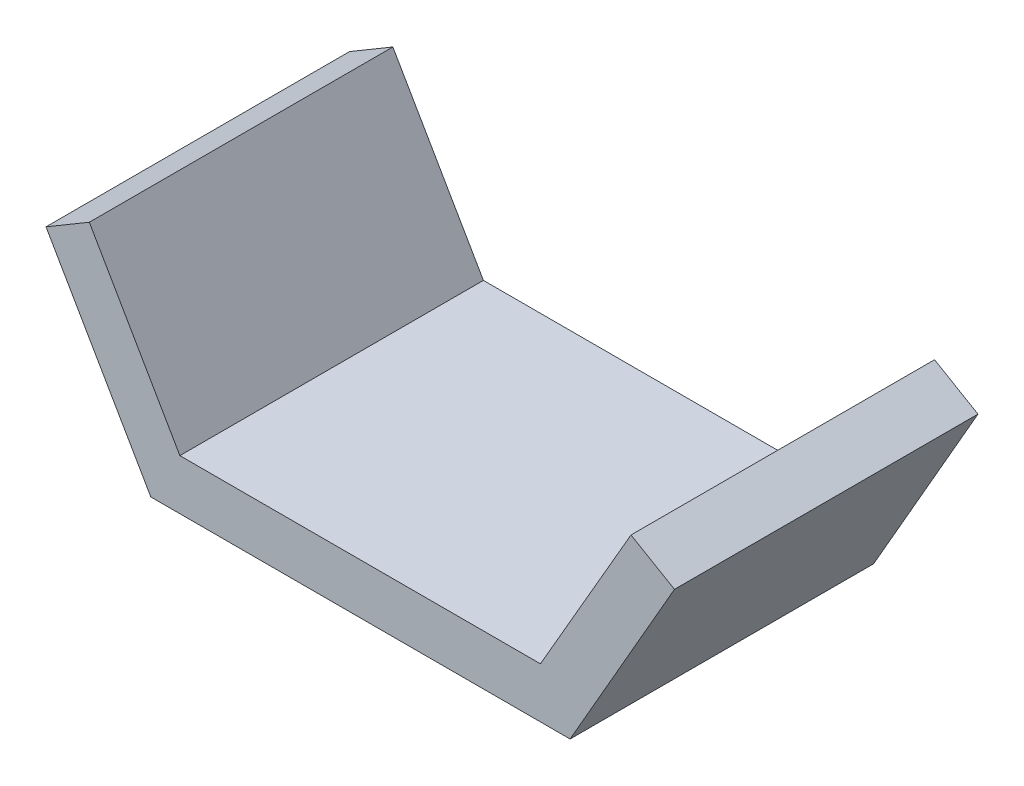
SolidWorks part; units mm, degrees
ref_plane "Alzado" through (0, 0, 0) normal (0, 0, 1) x (1, 0, 0)
ref_plane "Planta" through (0, 0, 0) normal (0, 1, 0) x (1, 0, 0)
ref_plane "Vista lateral" through (0, 0, 0) normal (1, 0, 0) x (0, 0, -1)
sketch "Croquis1" plane through (0, 0, 0) normal (0, 0, 1) x (1, 0, 0)
  line L8 (-113.3457, -408.1893) -> (2036.6543, -408.1893)
  line L9 (-113.3457, -408.1893) -> (-653.3457, 527.1182)
  line L10 (-653.3457, 527.1182) -> (-911.5508, 374.3425)
  line L11 (-911.5508, 374.3425) -> (-286.5508, -708.1893)
  line L12 (-286.5508, -708.1893) -> (2213.4492, -708.1893)
  line L13 (2213.4492, -708.1893) -> (2835.752, 375.8952)
  line L14 (2835.752, 375.8952) -> (2576.6543, 527.1182)
  line L15 (2576.6543, 527.1182) -> (2036.6543, -408.1893)
  point P2 (-667.2584, 608.9352)
  point P9 (-531.8495, 707.7471)
  dimension "D1" = 2150
  dimension "D2" = 2500
  dimension "D3" = 1250
  dimension "D4" = 1250
  dimension "D5" = 1080
  dimension "D6" = 1080
  dimension "D7" = 300
  dimension "D8" = 300
  dimension "D9" = 120
  dimension "D10" = 120
  dimension "D11" = 300
extrude "Saliente-Extruir1" add sketch "Croquis1" along normal blind 1810
